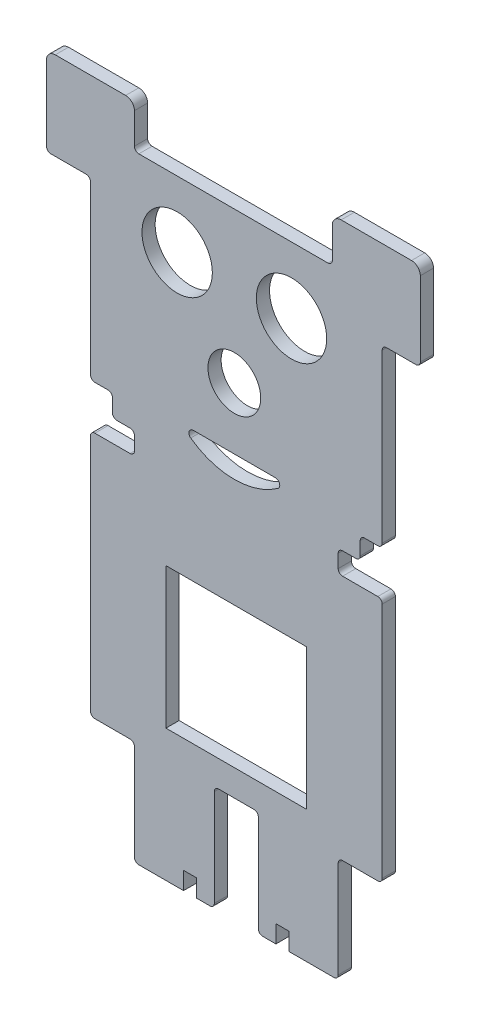
SolidWorks part; units mm, degrees
ref_plane "Alzado" through (0, 0, 0) normal (0, 0, 1) x (1, 0, 0)
ref_plane "Planta" through (0, 0, 0) normal (0, 1, 0) x (1, 0, 0)
ref_plane "Vista lateral" through (0, 0, 0) normal (1, 0, 0) x (0, 0, -1)
sketch "Model" plane through (0, 0, 0) normal (0, 0, 1) x (1, 0, 0)
  line L0 (12.9856, 18.252) -> (29.4856, 18.252)
  line L1 (12.9856, -13.748) -> (12.9856, 18.252)
  line L2 (44.9856, -13.748) -> (12.9856, -13.748)
  line L3 (44.9856, 18.252) -> (44.9856, -13.748)
  line L4 (29.4856, 18.252) -> (44.9856, 18.252)
  line L5 (37.8632, 48.0006) -> (19.2026, 48.0006)
  line L6 (52.1492, 40.252) -> (52.1492, 37.252)
  line L7 (56.1492, 41.252) -> (53.1492, 41.252)
  line L8 (57.1492, 45.252) -> (57.1492, 42.252)
  line L9 (61.1492, 46.252) -> (58.1492, 46.252)
  line L10 (62.1492, 12.6366) -> (62.1492, 35.252)
  line L11 (53.1492, 36.252) -> (61.1492, 36.252)
  line L12 (62.1492, 66.752) -> (62.1492, 47.252)
  line L13 (62.1492, 85.252) -> (62.1492, 66.752)
  line L14 (69.822, 86.252) -> (63.1492, 86.252)
  line L15 (70.822, 104.252) -> (70.822, 87.252)
  line L16 (62.1492, 12.6366) -> (62.1492, -18.748)
  line L17 (-4.178, 35.252) -> (-4.178, 14.6411)
  line L18 (53.1492, -19.748) -> (61.1492, -19.748)
  line L19 (52.1492, -42.748) -> (52.1492, -20.748)
  line L20 (40.9856, -43.748) -> (51.1492, -43.748)
  line L21 (40.9856, -39.748) -> (40.9856, -43.748)
  line L22 (37.9856, -39.748) -> (40.9856, -39.748)
  line L23 (37.9856, -43.748) -> (37.9856, -39.748)
  line L24 (34.9856, -43.748) -> (37.9856, -43.748)
  line L25 (33.9856, -20.748) -> (33.9856, -42.748)
  line L26 (24.9856, -19.748) -> (32.9856, -19.748)
  line L27 (23.9856, -42.748) -> (23.9856, -20.748)
  line L28 (19.9856, -43.748) -> (22.9856, -43.748)
  line L29 (19.9856, -39.748) -> (19.9856, -43.748)
  line L30 (16.9856, -39.748) -> (19.9856, -39.748)
  line L31 (16.9856, -43.748) -> (16.9856, -39.748)
  line L32 (6.822, -43.748) -> (16.9856, -43.748)
  line L33 (5.822, -20.9697) -> (5.822, -42.748)
  line L34 (-3.178, -19.9697) -> (4.822, -19.9697)
  line L35 (-4.178, 14.6411) -> (-4.178, -18.9697)
  line L36 (-13.178, 86.252) -> (-8.678, 86.252)
  line L37 (-14.178, 104.252) -> (-14.178, 87.252)
  line L38 (3.822, 106.252) -> (-12.178, 106.252)
  line L39 (5.822, 97.252) -> (5.822, 104.252)
  line L40 (49.822, 96.252) -> (6.822, 96.252)
  line L41 (50.822, 104.252) -> (50.822, 97.252)
  line L42 (68.822, 106.252) -> (52.822, 106.252)
  line L43 (-4.178, 85.252) -> (-4.178, 47.252)
  line L44 (-8.678, 86.252) -> (-5.178, 86.252)
  line L45 (4.822, 36.252) -> (-3.178, 36.252)
  line L46 (5.822, 40.252) -> (5.822, 37.252)
  line L47 (1.822, 41.252) -> (4.822, 41.252)
  line L48 (0.822, 45.252) -> (0.822, 42.252)
  line L49 (-3.178, 46.252) -> (-0.178, 46.252)
  circle A0 centre (28.5329, 62.0006) radius 6
  arc A1 (19.2026, 48.0006) -> (18.6198, 46.188) centre (19.2026, 47.0006) ccw
  arc A2 (38.446, 46.188) -> (37.8632, 48.0006) centre (37.8632, 47.0006) ccw
  arc A3 (18.6198, 46.188) -> (38.446, 46.188) centre (28.5329, 60.0096) ccw
  arc A4 (52.1492, 37.252) -> (53.1492, 36.252) centre (53.1492, 37.252) ccw
  arc A5 (53.1492, 41.252) -> (52.1492, 40.252) centre (53.1492, 40.252) ccw
  arc A6 (56.1492, 41.252) -> (57.1492, 42.252) centre (56.1492, 42.252) ccw
  arc A7 (58.1492, 46.252) -> (57.1492, 45.252) centre (58.1492, 45.252) ccw
  arc A8 (61.1492, 46.252) -> (62.1492, 47.252) centre (61.1492, 47.252) ccw
  arc A9 (62.1492, 35.252) -> (61.1492, 36.252) centre (61.1492, 35.252) ccw
  arc A10 (63.1492, 86.252) -> (62.1492, 85.252) centre (63.1492, 85.252) ccw
  arc A11 (69.822, 86.252) -> (70.822, 87.252) centre (69.822, 87.252) ccw
  arc A12 (61.1492, -19.748) -> (62.1492, -18.748) centre (61.1492, -18.748) ccw
  arc A13 (53.1492, -19.748) -> (52.1492, -20.748) centre (53.1492, -20.748) ccw
  arc A14 (51.1492, -43.748) -> (52.1492, -42.748) centre (51.1492, -42.748) ccw
  arc A15 (33.9856, -42.748) -> (34.9856, -43.748) centre (34.9856, -42.748) ccw
  arc A16 (33.9856, -20.748) -> (32.9856, -19.748) centre (32.9856, -20.748) ccw
  arc A17 (24.9856, -19.748) -> (23.9856, -20.748) centre (24.9856, -20.748) ccw
  arc A18 (22.9856, -43.748) -> (23.9856, -42.748) centre (22.9856, -42.748) ccw
  arc A19 (5.822, -42.748) -> (6.822, -43.748) centre (6.822, -42.748) ccw
  arc A20 (5.822, -20.9697) -> (4.822, -19.9697) centre (4.822, -20.9697) ccw
  arc A21 (-4.178, -18.9697) -> (-3.178, -19.9697) centre (-3.178, -18.9697) ccw
  arc A22 (-14.178, 87.252) -> (-13.178, 86.252) centre (-13.178, 87.252) ccw
  arc A23 (-12.178, 106.252) -> (-14.178, 104.252) centre (-12.178, 104.252) ccw
  arc A24 (5.822, 104.252) -> (3.822, 106.252) centre (3.822, 104.252) ccw
  arc A25 (5.822, 97.252) -> (6.822, 96.252) centre (6.822, 97.252) ccw
  arc A26 (49.822, 96.252) -> (50.822, 97.252) centre (49.822, 97.252) ccw
  arc A27 (52.822, 106.252) -> (50.822, 104.252) centre (52.822, 104.252) ccw
  arc A28 (70.822, 104.252) -> (68.822, 106.252) centre (68.822, 104.252) ccw
  arc A29 (-4.178, 85.252) -> (-5.178, 86.252) centre (-5.178, 85.252) ccw
  arc A30 (-3.178, 36.252) -> (-4.178, 35.252) centre (-3.178, 35.252) ccw
  arc A31 (4.822, 36.252) -> (5.822, 37.252) centre (4.822, 37.252) ccw
  arc A32 (5.822, 40.252) -> (4.822, 41.252) centre (4.822, 40.252) ccw
  arc A33 (0.822, 42.252) -> (1.822, 41.252) centre (1.822, 42.252) ccw
  arc A34 (0.822, 45.252) -> (-0.178, 46.252) centre (-0.178, 45.252) ccw
  arc A35 (-4.178, 47.252) -> (-3.178, 46.252) centre (-3.178, 47.252) ccw
  circle A36 centre (41.5329, 81.2006) radius 8
  circle A37 centre (15.5329, 81.2006) radius 8
extrude "Saliente-Extruir1" add sketch "Model" along normal blind 3
